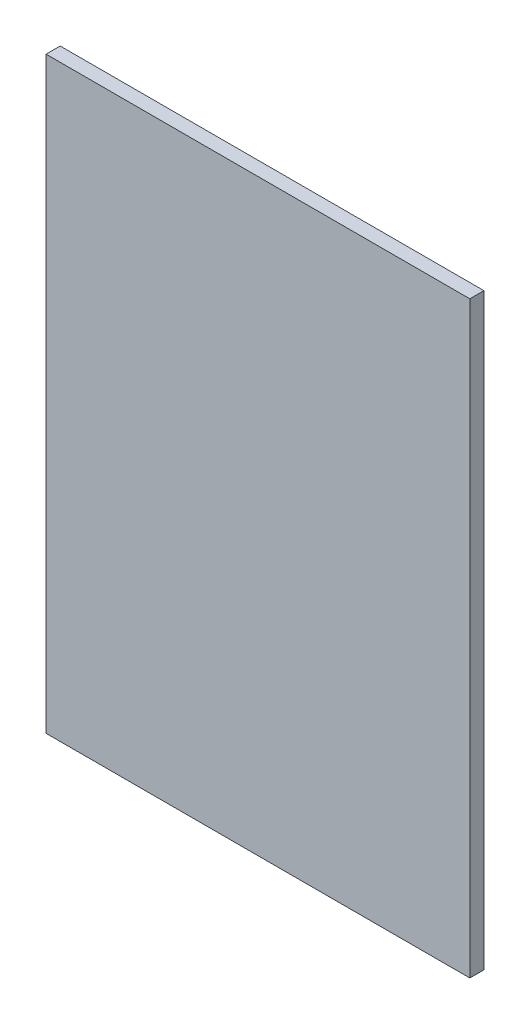
SolidWorks part; units mm, degrees
ref_plane "前视基准面" through (0, 0, 0) normal (0, 0, 1) x (1, 0, 0)
ref_plane "上视基准面" through (0, 0, 0) normal (0, 1, 0) x (1, 0, 0)
ref_plane "右视基准面" through (0, 0, 0) normal (1, 0, 0) x (0, 0, -1)
sketch "草图1" plane through (0, 0, 0) normal (0, 0, 1) x (1, 0, 0)
  line L0 (-348.5428, 33.2612) -> (-48.5428, 33.2612)
  line L1 (-48.5428, 33.2612) -> (-48.5428, 449.6885)
  line L2 (-48.5428, 449.6885) -> (-348.5428, 449.6885)
  line L3 (-348.5428, 449.6885) -> (-348.5428, 33.2612)
extrude "凸台-拉伸1" add sketch "草图1" along normal blind 10
